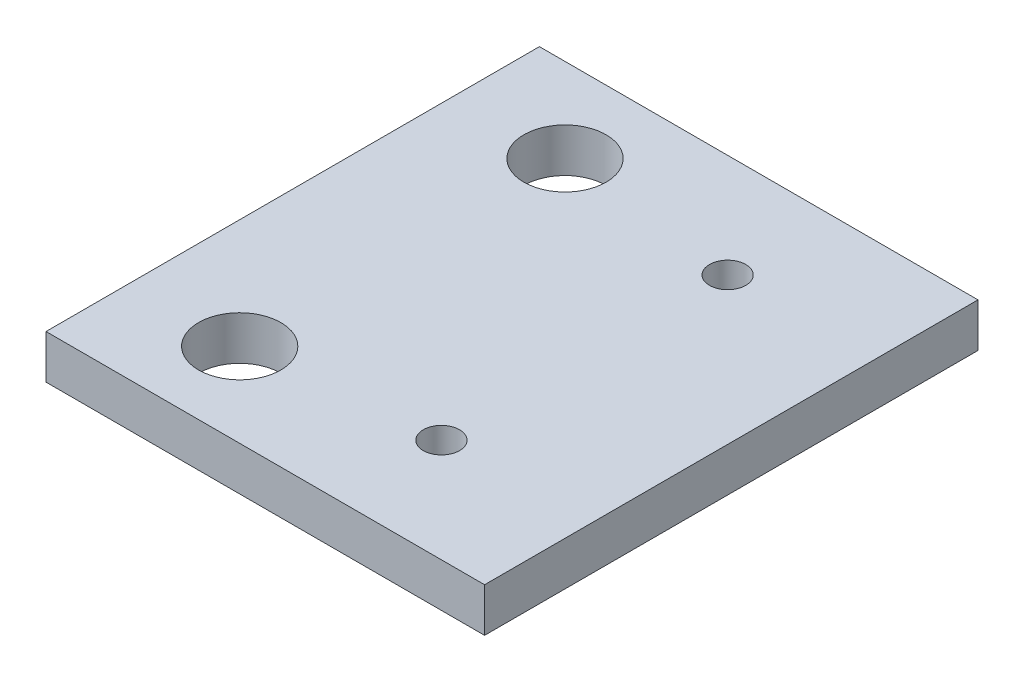
SolidWorks part; units mm, degrees
ref_plane "Front Plane" through (0, 0, 0) normal (0, 0, 1) x (1, 0, 0)
ref_plane "Top Plane" through (0, 0, 0) normal (0, 1, 0) x (1, 0, 0)
ref_plane "Right Plane" through (0, 0, 0) normal (1, 0, 0) x (0, 0, -1)
sketch "Sketch1" plane through (0, 0, 0) normal (0, 1, 0) x (1, 0, 0)
  line L1 (-25.4, 28.575) -> (25.4, 28.575)
  line L2 (-25.4, 28.575) -> (-25.4, -28.575)
  line L3 (-25.4, -28.575) -> (25.4, -28.575)
  line L4 (25.4, 28.575) -> (25.4, -28.575)
  line L5 (-25.4, 28.575) -> (25.4, -28.575) construction
  line L6 (-25.4, -28.575) -> (25.4, 28.575) construction
  point P4 (0, 0)
  dimension "D1" = 50.8
  dimension "D2" = 57.15
extrude "Boss-Extrude1" add sketch "Sketch1" along normal blind 5.08
sketch "Sketch2" plane through (0, 5.08, 0) normal (0, 1, 0) x (1, 0, 0)
  line L0 (-12.7, -18.8377) -> (-12.7, 18.8377) construction
  line L3 (-25.4, 18.8377) -> (25.4, 18.8377) construction
  line L4 (-25.4, 28.575) -> (-25.4, -28.575) construction
  line L5 (25.4, -28.575) -> (25.4, 28.575) construction
  line L6 (-25.4, -18.8377) -> (25.4, -18.8377) construction
  line L7 (-12.7, 0) -> (25.4, 0) construction
  circle A0 centre (-12.7, 18.8377) radius 4.7625
  circle A1 centre (-12.7, -18.8377) radius 4.7625
  dimension "D2" = 9.525
  dimension "D1" = 9.525
  dimension "D3" = 37.6753
  dimension "D4" = 38.1
extrude "Cut-Extrude1" cut sketch "Sketch2" against normal blind 5.08
sketch "Sketch3" plane through (0, 0, 0) normal (0, -1, 0) x (1, 0, 0)
  circle A0 centre (8.4, -16.575) radius 2.1 construction
  circle A1 centre (8.4, -16.575) radius 2.1
  circle A2 centre (8.4, 16.575) radius 2.1 construction
  circle A3 centre (8.4, 16.575) radius 2.1
extrude "Cut-Extrude3" cut sketch "Sketch3" against normal through all
